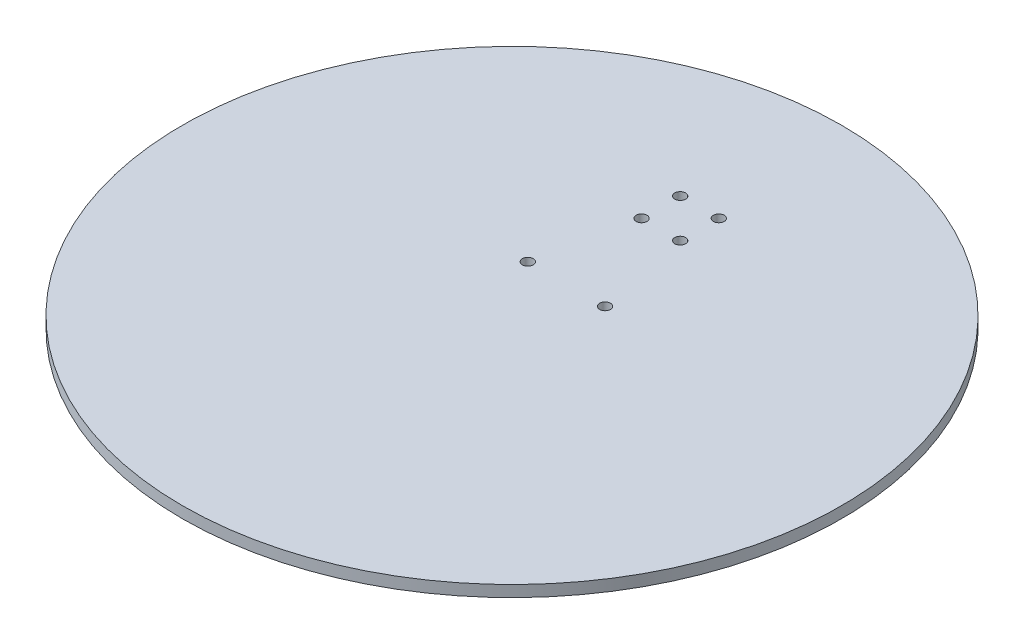
SolidWorks part; units mm, degrees
ref_plane "Front Plane" through (0, 0, 0) normal (0, 0, 1) x (1, 0, 0)
ref_plane "Top Plane" through (0, 0, 0) normal (0, 1, 0) x (1, 0, 0)
ref_plane "Right Plane" through (0, 0, 0) normal (1, 0, 0) x (0, 0, -1)
sketch "Sketch1" plane through (0, 0, 0) normal (0, 1, 0) x (1, 0, 0)
  line L0 (-16, 22.54) -> (16, 22.54) construction
  line L1 (-8, 77.66) -> (8, 77.66) construction
  line L2 (-8, 77.66) -> (-8, 61.66) construction
  line L3 (-8, 61.66) -> (8, 61.66) construction
  line L4 (8, 77.66) -> (8, 61.66) construction
  line L5 (-8, 77.66) -> (8, 61.66) construction
  line L6 (-8, 61.66) -> (8, 77.66) construction
  line L7 (-39.6975, 46.5) -> (42.5685, 46.5) construction
  line L9 (-12, 81.66) -> (12, 81.66) construction
  line L10 (-12, 81.66) -> (-12, 57.66) construction
  line L11 (-12, 57.66) -> (12, 57.66) construction
  line L12 (12, 81.66) -> (12, 57.66) construction
  line L13 (-12, 81.66) -> (12, 57.66) construction
  line L14 (-12, 57.66) -> (12, 81.66) construction
  circle A0 centre (0, 0) radius 136.5
  circle A1 centre (-8, 77.66) radius 2.25
  circle A2 centre (8, 77.66) radius 2.25
  circle A3 centre (8, 61.66) radius 2.25
  circle A4 centre (-8, 61.66) radius 2.25
  circle A5 centre (-16, 22.54) radius 2.25
  circle A6 centre (16, 22.54) radius 2.25
  point P3 (0, 69.66)
  point P14 (0, 22.54)
  point P19 (0, 69.66)
  dimension "D1" = 273
  dimension "D3" = 4.5
  dimension "D5" = 4.5
  dimension "D2" = 16
  dimension "D4" = 32
  dimension "D6" = 46.5
  dimension "D7" = 23.96
  dimension "D8" = 24
  dimension "D9" = 11.16
extrude "Boss-Extrude1" add sketch "Sketch1" along normal blind 4.7
equation "\"D7@Sketch1\"=12+3.96+8"
